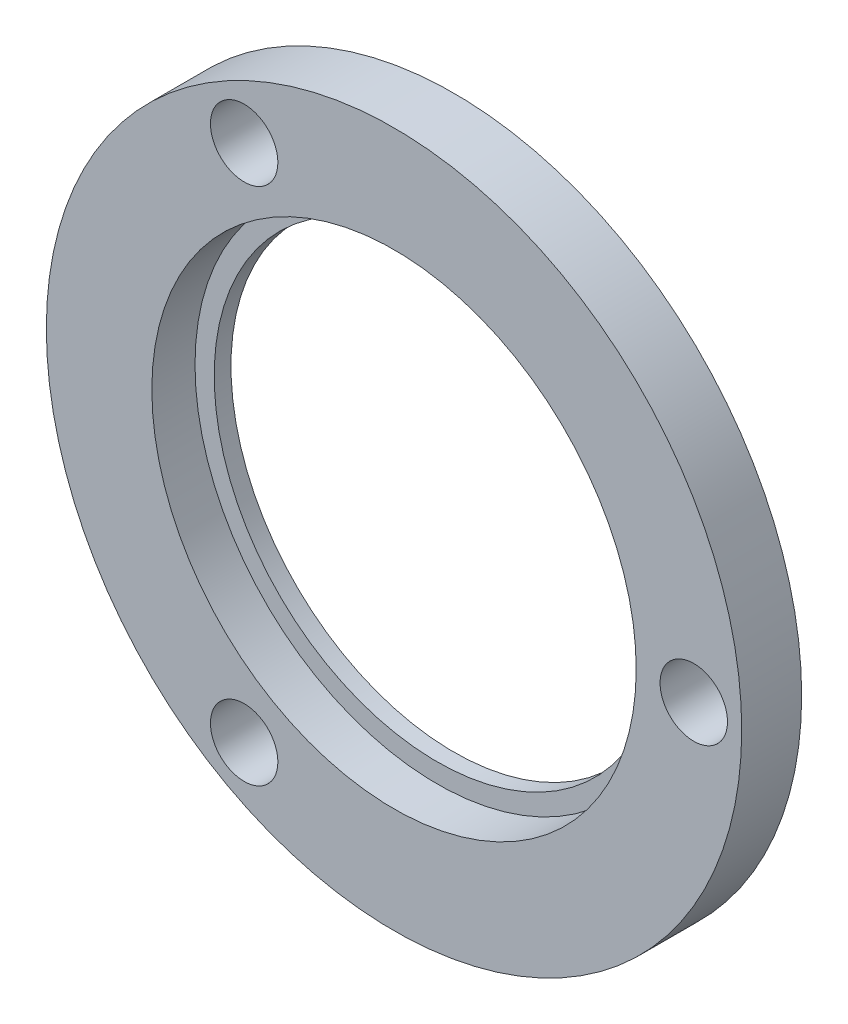
SolidWorks part; units mm, degrees
material "6061-T6 Al"
ref_plane "Front" through (0, 0, 0) normal (0, 0, 1) x (1, 0, 0)
ref_plane "Top" through (0, 0, 0) normal (0, 1, 0) x (1, 0, 0)
ref_plane "Right" through (0, 0, 0) normal (1, 0, 0) x (0, 0, -1)
sketch "Sketch" plane through (0, 0, 0) normal (0, 0, 1) x (1, 0, 0)
  line L2 (0, 0) -> (31.75, 0) construction
  circle A0 centre (0, 0) radius 25.654 construction
  circle A2 centre (0, 0) radius 36.83
  circle A3 centre (31.75, 0) radius 3.175 construction
  circle A21 centre (0, 0) radius 23.622
  point P5 (-25.908, 20.828)
  point P6 (25.908, 20.828)
  point P7 (25.908, -20.828)
  point P8 (-25.908, -20.828)
  point P63 (-25.781, -19.05)
  point P64 (25.781, -19.05)
  dimension "D5" = 47.244
  dimension "D3" = 73.66
  dimension "D4" = 6.35
  dimension "D1" = 31.75
  dimension "D2" = 51.308
extrude "Boss-Extrude1" add sketch "Sketch" against normal blind 6.35
sketch "Sketch1" plane through (0, 0, 0) normal (0, 0, 1) x (1, 0, 0)
  circle A0 centre (0, 0) radius 25.654 construction
  circle A1 centre (0, 0) radius 25.654
extrude "Cut-Extrude1" cut sketch "Sketch1" against normal offset from surface (4.572 mm away) 1.778 up to face at (23.622, 0, -6.35)
hole_wizard "1/4 Clearance Hole1" positions "Sketch3" profile "Sketch2" hole size "1/4" standard "ANSI Inch" end condition through all
sketch "Sketch3" plane through (0, 0, 0) normal (0, 0, 1) x (1, 0, 0)
  point P0 (31.75, 0)
  point P7 (-15.875, -27.4963)
  point P8 (-15.875, 27.4963)
  dimension "D1" = 3
sketch "Sketch2" plane through (31.75, 0, 0) normal (1, 0, 0) x (0, -1, 0)
  line L0 (0, 0) -> (0, 6.35)
  line L1 (0, 6.35) -> (3.5712, 6.35)
  line L2 (3.5712, 6.35) -> (3.5712, 0)
  line L5 (3.5712, 0) -> (0, 0)
  line L11 (0, -6.35) -> (0, 107.95) construction
  dimension "Thru Hole Dia." = 7.1425
  dimension "Thru Hole Depth" = 6.35
